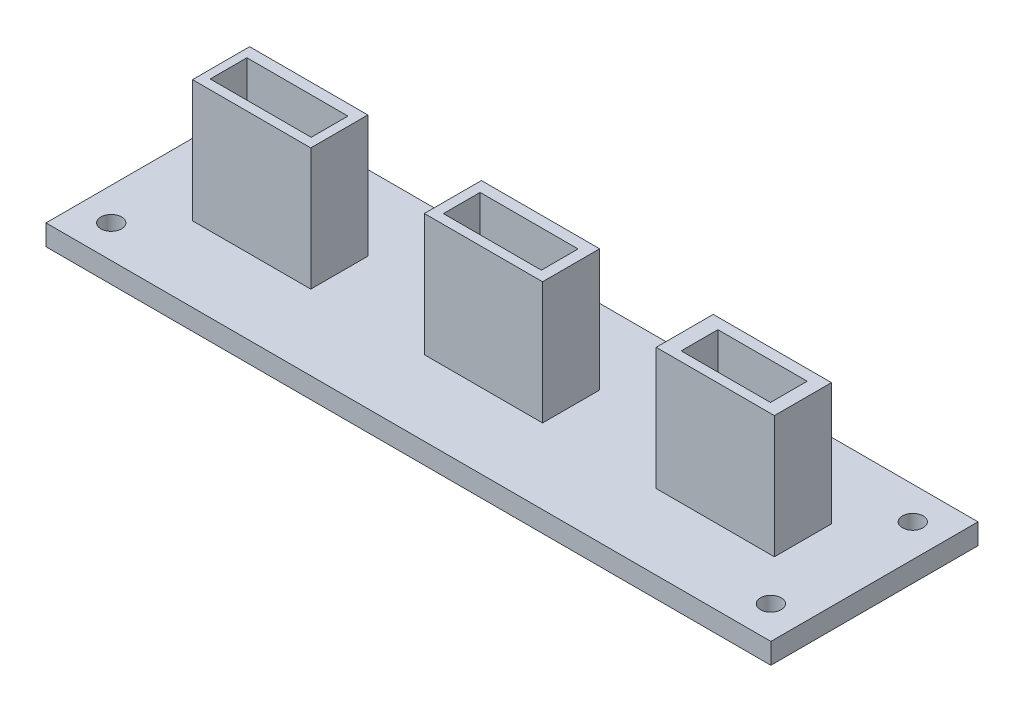
SolidWorks part; units mm, degrees
ref_plane "Front Plane" through (0, 0, 0) normal (0, 0, 1) x (1, 0, 0)
ref_plane "Top Plane" through (0, 0, 0) normal (0, 1, 0) x (1, 0, 0)
ref_plane "Right Plane" through (0, 0, 0) normal (1, 0, 0) x (0, 0, -1)
sketch "Sketch1" plane through (0, 0, 0) normal (0, 1, 0) x (1, 0, 0)
  line L0 (-55, 0) -> (55, 0) construction
  line L1 (-44.45, 12.7) -> (44.45, 12.7)
  line L2 (-44.45, 12.7) -> (-44.45, -12.7)
  line L3 (-44.45, -12.7) -> (44.45, -12.7)
  line L4 (44.45, 12.7) -> (44.45, -12.7)
  line L5 (0, -55) -> (0, 55) construction
  dimension "D1" = 88.9
  dimension "D2" = 25.4
  dimension "D3" = 12.7
  dimension "D4" = 44.45
extrude "Boss-Extrude1" add sketch "Sketch1" along normal blind 2.54
sketch "Sketch2" plane through (0, 2.54, 0) normal (0, 1, 0) x (1, 0, 0)
  line L0 (44.45, 12.7) -> (-44.45, 12.7) construction
  line L1 (-44.45, 12.7) -> (-44.45, -12.7) construction
  line L2 (-44.45, -12.7) -> (44.45, -12.7) construction
  line L3 (44.45, -12.7) -> (44.45, 12.7) construction
  circle A0 centre (-40.45, 8.7) radius 1.27
  circle A1 centre (-40.45, -8.7) radius 1.27
  circle A2 centre (40.45, -8.7) radius 1.27
  circle A3 centre (40.45, 8.7) radius 1.27
  dimension "D1" = 2.54
  dimension "D4" = 2.54
  dimension "D7" = 2.54
  dimension "D10" = 2.54
  dimension "D2" = 4
  dimension "D3" = 4
  dimension "D5" = 4
  dimension "D6" = 4
  dimension "D8" = 4
  dimension "D9" = 4
  dimension "D11" = 4
  dimension "D12" = 4
extrude "Cut-Extrude1" cut sketch "Sketch2" against normal blind 2.54
sketch "Sketch16" plane through (0, 2.54, 0) normal (0, 1, 0) x (1, 0, 0)
  line L0 (0, -13.97) -> (0, 13.97) construction
  line L1 (-7.25, 3.5) -> (7.25, 3.5)
  line L2 (-7.25, 3.5) -> (-7.25, -3.5)
  line L3 (-7.25, -3.5) -> (7.25, -3.5)
  line L4 (7.25, 3.5) -> (7.25, -3.5)
  line L5 (-15.235, 0) -> (15.235, 0) construction
  line L6 (21.18, 3.5) -> (35.68, 3.5)
  line L7 (21.18, 3.5) -> (21.18, -3.5)
  line L8 (21.18, -3.5) -> (35.68, -3.5)
  line L9 (35.68, 3.5) -> (35.68, -3.5)
  line L10 (-35.68, 3.5) -> (-21.18, 3.5)
  line L11 (-35.68, 3.5) -> (-35.68, -3.5)
  line L12 (-35.68, -3.5) -> (-21.18, -3.5)
  line L13 (-21.18, 3.5) -> (-21.18, -3.5)
  dimension "D1" = 14.5
  dimension "D2" = 7.25
  dimension "D3" = 7
  dimension "D4" = 3.5
  dimension "D5" = 14.5
  dimension "D6" = 7
  dimension "D7" = 13.93
  dimension "D8" = 3.5
  dimension "D9" = 14.5
  dimension "D10" = 7
  dimension "D11" = 13.93
  dimension "D12" = 3.5
extrude "Boss-Extrude3" add sketch "Sketch16" along normal blind 15
sketch "Sketch17" plane through (0, 17.54, 0) normal (0, 1, 0) x (1, 0, 0)
  line L1 (-34.6693, 2.159) -> (-22.2785, 2.159)
  line L2 (-34.6693, 2.159) -> (-34.6693, -2.3467)
  line L3 (-34.6693, -2.3467) -> (-22.2785, -2.3467)
  line L4 (-22.2785, 2.159) -> (-22.2785, -2.3467)
  line L5 (-6.0703, 2.159) -> (5.9451, 2.159)
  line L6 (-6.0703, 2.159) -> (-6.0703, -2.3467)
  line L7 (-6.0703, -2.3467) -> (5.9451, -2.3467)
  line L8 (5.9451, 2.159) -> (5.9451, -2.3467)
  line L9 (23.092, 2.159) -> (34.0435, 2.159)
  line L10 (23.092, 2.159) -> (23.092, -2.3467)
  line L11 (23.092, -2.3467) -> (34.0435, -2.3467)
  line L12 (34.0435, 2.159) -> (34.0435, -2.3467)
extrude "Cut-Extrude4" cut sketch "Sketch17" against normal blind 12.46
sketch "Sketch18" plane through (0, 5.08, 0) normal (0, 1, 0) x (1, 0, 0)
  line L0 (-9.7174, 0) -> (9.7174, 0) construction
  circle A0 centre (-33.3551, 0) radius 0.8654
  circle A1 centre (-30.2887, 0) radius 0.972
  circle A2 centre (-27.5352, 0) radius 0.9387
  circle A3 centre (-24.9068, 0) radius 1.023
  circle A4 centre (-4.5062, -1.023) radius 0.6999
  circle A5 centre (-1.8737, -1.023) radius 0.7249
  circle A6 centre (0.7277, -1.023) radius 0.7532
  circle A7 centre (3.7904, -1.023) radius 0.8939
  circle A8 centre (25.7833, -1.023) radius 0.6844
  circle A9 centre (28.074, -1.023) radius 0.9066
  circle A10 centre (30.3542, -1.023) radius 0.7743
  circle A11 centre (32.4134, -1.023) radius 0.7398
extrude "Cut-Extrude5" cut sketch "Sketch18" against normal blind 12.46
